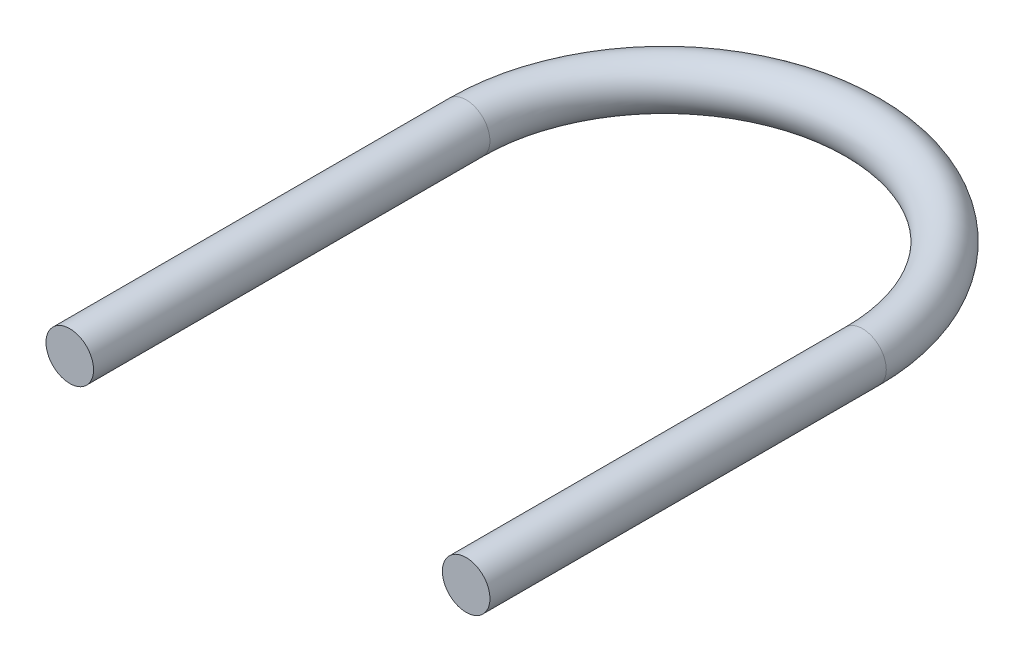
SolidWorks part; units mm, degrees
material "1.0553 (S355J0)"
ref_plane "Płaszczyzna przednia" through (0, 0, 0) normal (0, 0, 1) x (1, 0, 0)
ref_plane "Płaszczyzna górna" through (0, 0, 0) normal (0, 1, 0) x (1, 0, 0)
ref_plane "Płaszczyzna prawa" through (0, 0, 0) normal (1, 0, 0) x (0, 0, -1)
sketch "Szkic1" plane through (0, 0, 0) normal (0, 1, 0) x (1, 0, 0)
  line L0 (-25, 0) -> (-25, -50)
  line L1 (25, 0) -> (25, -50)
  arc A0 (25, 0) -> (-25, 0) centre (0, 0) ccw
  dimension "D1" = 25
  dimension "D2" = 50
ref_plane "Płaszczyzna1" through (0, 0, 50) normal (0, 0, 1) x (1, 0, 0)
sketch "Szkic2" plane through (0, 0, 50) normal (0, 0, 1) x (1, 0, 0)
  line L0 (25, 0) -> (-25, 0) construction
  circle A0 centre (-25, 0) radius 3
  dimension "D1" = 6
sweep "Wyciągnięcie po ścieżce1" add profiles "Szkic2" path "Szkic1"
